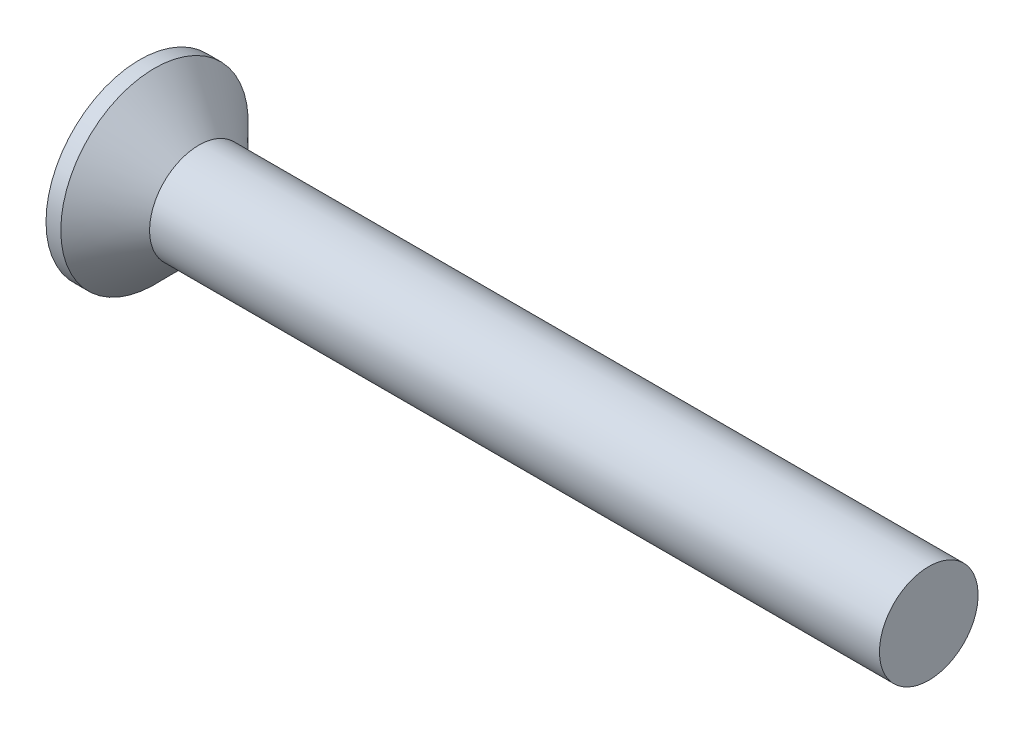
SolidWorks part; units mm, degrees
ref_plane "Plane1" through (0, 0, 0) normal (0, 0, 1) x (1, 0, 0)
ref_plane "Plane2" through (0, 0, 0) normal (0, 1, 0) x (1, 0, 0)
ref_plane "Plane3" through (0, 0, 0) normal (1, 0, 0) x (0, 0, -1)
sketch "BodySke" plane through (0, 0, 0) normal (0, 0, 1) x (1, 0, 0)
  line L0 (0, 0) -> (0, 1.9)
  line L1 (0, 1.9) -> (0.3, 1.9)
  line L2 (1.2, 1) -> (16, 1)
  line L3 (16, 1) -> (16, 0)
  line L4 (16, 0) -> (0, 0)
  line L5 (-6.35, 0) -> (82.55, 0) construction
  line L6 (1.2, -1) -> (16, -1) construction
  line L7 (0.3, -1.9) -> (1.2, -1) construction
  line L8 (0.3, 1.9) -> (1.2, 1)
  line L9 (0, -1.9) -> (0.3, -1.9) construction
  line L10 (1.6, 2.5875) -> (1.6, -6.9375) construction
  line L11 (0, 6.35) -> (0, -3.175) construction
  dimension "Diameter" = 2
  dimension "Length" = 16
  dimension "Head_ht" = 1.2
  dimension "Head_dia" = 3.8
  dimension "Head_ang" = 90
  dimension "D6" = 0.3
  dimension "Advance" = 0.4
  dimension "Thread_nom" = 16
revolve "Base-Revolve" add sketch "BodySke" angle 360 about L5
cosmetic thread "ThreadCosmetic" [suppressed] parameters "Thread_length"=14.4, "Thread_minor"=1.548
sketch "Sketch2" plane through (0, 0, 0) normal (-1, 0, 0) x (0, 0, 1)
  line L0 (-1.9, -0.35) -> (1.9, -0.35)
  line L1 (-1.9, -0.35) -> (-1.9, 0.35)
  line L2 (1.9, 0.35) -> (-1.9, 0.35)
  line L3 (1.9, 0.35) -> (1.9, -0.35)
  dimension "D1" = 0.35
  dimension "Slot_width" = 0.7
  dimension "D2" = 3.8
  dimension "D3" = 1.9
extrude "Slot" [suppressed] cut sketch "Sketch2" against normal blind 0.6
sketch "Sketch3" plane through (0, 0, 0) normal (-1, 0, 0) x (0, 0, 1)
  line L0 (-0.265, 1.07) -> (0.265, 1.07)
  line L1 (0.265, 1.07) -> (0.265, -1.07)
  line L2 (0.265, -1.07) -> (-0.265, -1.07)
  line L3 (-0.265, -1.07) -> (-0.265, 1.07)
  dimension "D1" = 1.07
  dimension "Cross_dia" = 2.14
  dimension "D2" = 0.265
  dimension "Cross_width" = 0.53
ref_plane "Plane4" through (1.54, 0, 0) normal (-1, 0, 0) x (0, 0, 1)
sketch "Sketch4" plane through (1.54, 0, 0) normal (-1, 0, 0) x (0, 0, 1)
  line L0 (-0.1325, 0.1325) -> (0.1325, 0.1325)
  line L3 (0.1325, 0.1325) -> (0.1325, -0.1325)
  line L4 (0.1325, -0.1325) -> (-0.1325, -0.1325)
  line L5 (-0.1325, -0.1325) -> (-0.1325, 0.1325)
  dimension "D1" = 0.265
  dimension "D2" = 0.265
  dimension "D3" = 0.1325
  dimension "D4" = 0.1325
loft "Cross" cut profiles "Sketch3", "Sketch4"
pattern_circular "CirPattern1" count 2 every 90 about axis through (0, 0, 0) along (1, 0, 0) of "Cross"
sketch "ThdSchSke" plane through (0, 0, 0) normal (0, 0, 1) x (1, 0, 0)
  line L0 (1.6, -0.774) -> (1.4418, -1)
  line L1 (1.6, -0.774) -> (1.7582, -1)
  line L2 (1.7582, -1) -> (1.7582, -1.25)
  line L3 (-3.175, 0) -> (5.1513, 0) construction
  line L5 (1.7582, -1.25) -> (1.4418, -1.25)
  line L6 (1.4418, -1.25) -> (1.4418, -1)
  line L7 (0, 1.9) -> (0, -1.9) construction
  dimension "Thread_minor" = 1.548
  dimension "Diameter" = 2
  dimension "Start" = 1.6
  dimension "SideAngle" = 55
  dimension "VeeAngle" = 70
  dimension "Overcut" = 2.5
revolve "ThreadSchematic" [suppressed] cut sketch "ThdSchSke" angle 360 about L3
pattern_linear "ThdSchPat" [suppressed]
equation "\"D1@Sketch3\" = \"Cross_dia@Sketch3\" / 2"
equation "\"D2@Sketch3\" = \"Cross_width@Sketch3\" / 2"
equation "\"D1@Sketch4\" = \"Cross_width@Sketch3\" *.5"
equation "\"D2@Sketch4\" = \"D1@Sketch4\""
equation "\"D4@Sketch4\" = \"D2@Sketch4\" / 2"
equation "\"D3@Sketch4\" = \"D1@Sketch4\" / 2"
equation "\"D1@Sketch2\" = \"Slot_width@Sketch2\" / 2"
equation "\"D2@Sketch2\" = \"Head_dia@BodySke\""
equation "\"D3@Sketch2\" = \"D2@Sketch2\" / 2"
equation "\"Thread_length@ThreadCosmetic\" = ((sgn( (\"Length@BodySke\" - \"Advance@BodySke\" - \"Head_ht@BodySke\" ) - \"Thread_nom@BodySke\" )-1)*( (\"Length@BodySke\" - \"Advance@BodySke\" - \"Head_ht@BodySke\" ) - \"Thread_nom@BodySke\" ))/-2+ \"Thread_nom@BodySke\""
equation "\"Thread_minor@ThdSchSke\" = \"Thread_minor@ThreadCosmetic\""
equation "\"Diameter@ThdSchSke\" = \"Diameter@BodySke\""
equation "\"Overcut@ThdSchSke\" = \"Diameter@BodySke\" * 1.25"
equation "\"Start@ThdSchSke\" = 0.000001 + \"Length@BodySke\" - \"Thread_length@ThreadCosmetic\"  '---Countersunk---"
equation "\"Num_threads@ThdSchPat\" = int( \"Thread_length@ThreadCosmetic\" / \"Advance@BodySke\" + 0.999 )  + 1"
equation "\"Advance@ThdSchPat\" = \"Thread_length@ThreadCosmetic\" /  (\"Num_threads@ThdSchPat\" - 1) 'relax it"
